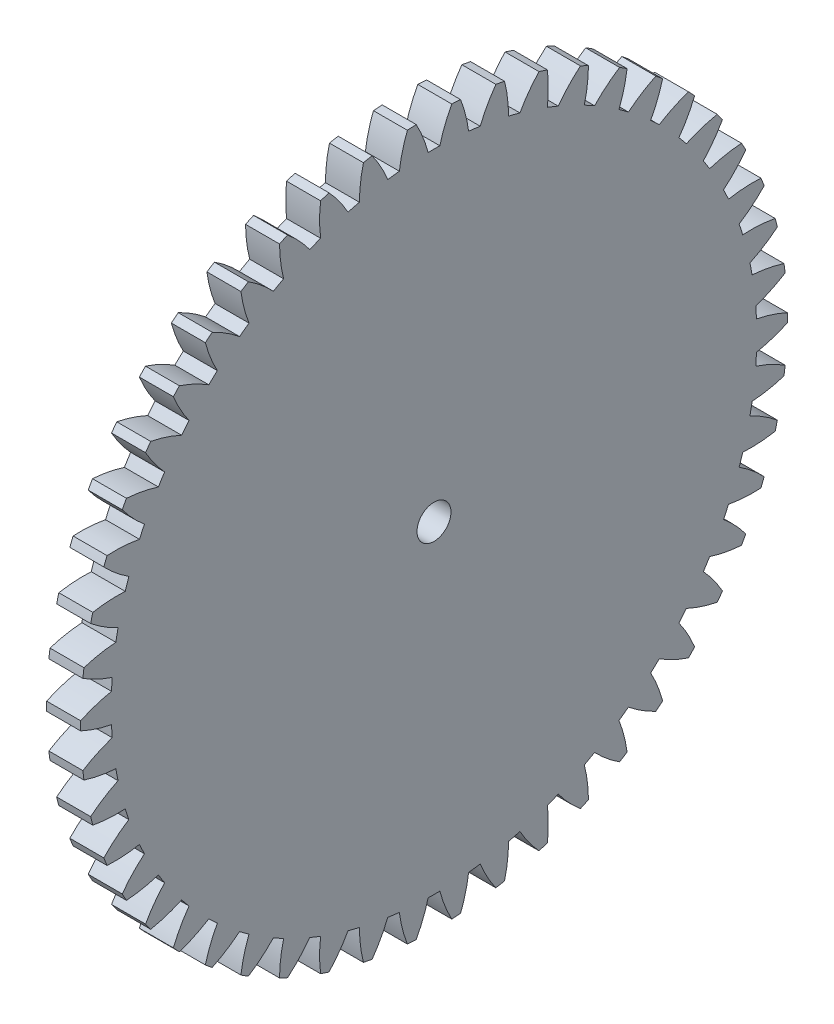
SolidWorks part; units mm, degrees
ref_plane "Plane1" through (0, 0, 0) normal (0, 0, 1) x (1, 0, 0)
ref_plane "Plane2" through (0, 0, 0) normal (0, 1, 0) x (1, 0, 0)
ref_plane "Plane3" through (0, 0, 0) normal (1, 0, 0) x (0, 0, -1)
sketch "HoldingSke" plane through (0, 0, 0) normal (0, 1, 0) x (1, 0, 0)
  line L0 (0, 0) -> (0.3214, -0.383)
  line L1 (-15, 0) -> (100, 0) construction
  line L2 (0, 0) -> (-2.1039, 2.3779)
  line L3 (0, 0) -> (-11.863, 4.5341)
  line L4 (0, 0) -> (5.5511, 6.6156)
  line L5 (0, 0) -> (-46.8476, -17.4728)
  line L6 (0, 0) -> (-4.1448, -2.7965)
  line L7 (-2.1039, 2.3779) -> (8.6586, 51.2059)
  line L8 (-76.2, 54.61) -> (-75.3, 54.61)
  line L9 (-71.009, 38.7566) -> (-53.1078, 45.2721)
  line L10 (-76.2, 71.12) -> (104.1128, 71.12)
  line L11 (0, 0) -> (-5, 0)
  line L12 (-76.2, 101.6) -> (-76.133, 101.6)
  line L13 (24.9733, 27.94) -> (52.9518, 28.4284)
  line L14 (24.9733, 27.94) -> (24.9743, 27.94)
  line L15 (24.9733, 27.94) -> (100.4006, 29.5858)
  line L16 (-63.627, -2) -> (-12.827, -2)
  circle A0 centre (0, 0) radius 2.5
  circle A1 centre (0, 0) radius 37.5
  circle A2 centre (0, 0) radius 37.5
  circle A3 centre (0, 0) radius 2.5
  dimension "MHD" = 75
  dimension "Hub_dia" = 75
  dimension "Bore" = 5
  dimension "MBD" = 5
  dimension "Num_teeth" = 50
  dimension "Pitch_radius" = 180.3128
  dimension "Pitch" = 0.5
  dimension "Width" = 5
  dimension "Overall_len" = 50
  dimension "Show_teeth" = 50
  dimension "Thickness" = 5
  dimension "OAL" = 50.0001
  dimension "T_dim" = 0.9
  dimension "Ap" = 20
  dimension "H" = 19.05
  dimension "Backlash" = 0.067
  dimension "Addendum_fac" = 1
  dimension "Dedendum_fac" = 1.25
  dimension "Clearance_fac" = 0.25
  dimension "Dedendum_add" = 0.001
  dimension "Module" = 2
sketch "BasProSke" plane through (0, 0, 0) normal (0, 1, 0) x (1, 0, 0)
  line L0 (-10, 0) -> (60, 0) construction
  line L1 (0, 0) -> (0, 52)
  line L2 (0, 0) -> (5, 0)
  line L3 (5, 0) -> (5, 52)
  line L4 (5, 52) -> (0, 52)
  dimension "Diameter" = 104
  dimension "Thickness" = 5
revolve "Base-Revolve" add sketch "BasProSke" angle 360 about L0
sketch "TooCutSke" plane through (0, 0, 0) normal (1, 0, 0) x (0, 0, -1)
  line L1 (0, 0) -> (0, 107) construction
  line L2 (0, 0) -> (-1.6878, 49.9715) construction
  line L3 (0, 0) -> (-6.2764, 99.7605) construction
  line L4 (-1.6878, 49.9715) -> (-3.1382, 49.8803) construction
  arc A0 (0.8606, 47.4912) -> (-0.8606, 47.4912) centre (0, 0) ccw
  arc A1 (2.629, 51.9589) -> (-2.629, 51.9589) centre (0, 0) ccw
  circle A2 centre (0, 0) radius 50 construction
  circle A3 centre (0, 0) radius 46.9846 construction
  arc A4 (-0.8606, 47.4912) -> (-2.629, 51.9589) centre (-20.2064, 42.4176) ccw
  arc A5 (2.629, 51.9589) -> (0.8606, 47.4912) centre (20.2064, 42.4176) ccw
  dimension "Root_dia" = 94.998
  dimension "Overcut_dia" = 104.0508
  dimension "Pitch_dia" = 100
  dimension "Base_dia" = 93.9693
  dimension "Flank_rad" = 20
  dimension "Half_ang" = 3.6
  dimension "Half_CT" = 1.4533
extrude "ToothCut" cut sketch "TooCutSke" along normal through all
fillet "Breaks" [suppressed] radius 0.04
fillet "RootFillets" [suppressed] radius 0.501
pattern_circular "TeethCuts" count 50 every 7.2 about axis through (-10, 0, 0) along (1, 0, 0) of "ToothCut", "RootFillets", "Breaks"
sketch "HubNeaOneSke" plane through (0, 0, 0) normal (-1, 0, 0) x (0, 0, 1)
  circle A0 centre (0, 0) radius 37.5
  dimension "Diameter" = 75
extrude "HubNearOne" [suppressed] add sketch "HubNeaOneSke" along normal blind 45.0001
sketch "HubNeaBotSke" plane through (0, 0, 0) normal (-1, 0, 0) x (0, 0, 1)
  circle A0 centre (0, 0) radius 37.5
  dimension "Diameter" = 75
extrude "HubNearBoth" [suppressed] add sketch "HubNeaBotSke" along normal blind 22.5
ref_plane "FarPln" through (5, 0, 0) normal (1, 0, 0) x (0, 0, -1)
sketch "HubFarSke" plane through (5, 0, 0) normal (1, 0, 0) x (0, 0, -1)
  circle A0 centre (0, 0) radius 37.5
  dimension "Diameter" = 75
extrude "HubFar" [suppressed] add sketch "HubFarSke" along normal blind 22.5
sketch "BorSke" plane through (0, 0, 0) normal (1, 0, 0) x (0, 0, -1)
  circle A0 centre (0, 0) radius 2.5
  dimension "Diameter" = 5
extrude "Bore" cut sketch "BorSke" along normal mid plane 100.0001
sketch "KeySke" plane through (0, 0, 0) normal (1, 0, 0) x (0, 0, -1)
  line L0 (-1, 0) -> (-1, 3.4)
  line L1 (-1, 3.4) -> (1, 3.4)
  line L2 (1, 3.4) -> (1, 0)
  line L3 (0, 0) -> (0, 34) construction
  line L4 (-1, 0) -> (1, 0)
  dimension "Offset" = 3.4
  dimension "Width" = 2
extrude "Keyway" [suppressed] cut sketch "KeySke" along normal mid plane 100.0001
pattern_circular "Keyway2" [suppressed] count 2 every 90 about axis through (-10, 0, 0) along (1, 0, 0)
equation "' \"Module@HoldingSke\" = 6.35"
equation "' \"Num_teeth@HoldingSke\" = 12"
equation "' \"Ap@HoldingSke\" =  20"
equation "' \"Width@HoldingSke\" = 0.5 * 25.4"
equation "' \"Hub_dia@HoldingSke\"= 1 * 25.4"
equation "' \"Overall_len@HoldingSke\" = 1.0 * 25.4"
equation "' \"Bore@HoldingSke\" = 0.75 * 25.4"
equation "' \"T_dim@HoldingSke\" = 0.1 * 25.4"
equation "' \"Width@KeySke\" = 0.25 * 25.4"
equation "' \"Show_teeth@HoldingSke\" = 13"
equation "' \"Backlash@HoldingSke\" = 0.009 * 25.4"
equation "' \"Addendum_fac@HoldingSke\" = 1.0"
equation "' \"Dedendum_fac@HoldingSke\" = 1.25"
equation "' \"Dedendum_add@HoldingSke\" = 0.00005 * 25.4"
equation "' \"Clearance_fac@HoldingSke\" = 0.25"
equation "\"Pitch@HoldingSke\" = 1 / \"Module@HoldingSke\""
equation "\"Overcut_dia@TooCutSke\" = (\"Num_teeth@HoldingSke\" + 2 * \"Addendum_fac@HoldingSke\") / \"Pitch@HoldingSke\" + 0.002 * 25.4"
equation "\"Pitch_dia@TooCutSke\" = \"Num_teeth@HoldingSke\" / \"Pitch@HoldingSke\""
equation "\"Base_dia@TooCutSke\" = \"Num_teeth@HoldingSke\" / \"Pitch@HoldingSke\" * cos((\"Ap@HoldingSke\"  * 3.14159265 / 180))"
equation "\"Root_dia@TooCutSke\" = (\"Num_teeth@HoldingSke\" + 2) / \"Pitch@HoldingSke\" - 2 * (\"Addendum_fac@HoldingSke\" + \"Dedendum_fac@HoldingSke\") / \"Pitch@HoldingSke\" - \"Dedendum_add@HoldingSke\" * 2"
equation "\"Half_ang@TooCutSke\" = 180 / \"Num_teeth@HoldingSke\""
equation "\"Half_CT@TooCutSke\" = \"Num_teeth@HoldingSke\" / \"Pitch@HoldingSke\" * sin((3.14159265 / 2 / \"Num_teeth@HoldingSke\")) / 2 - 7 * \"Backlash@HoldingSke\" / 4"
equation "\"Flank_rad@TooCutSke\" = \"Num_teeth@HoldingSke\" / \"Pitch@HoldingSke\" / 5"
equation "\"Radius@RootFillets\" = \"Clearance_fac@HoldingSke\" / \"Pitch@HoldingSke\" + \"Dedendum_add@HoldingSke\""
equation "\"Break_rad@Breaks\" = 0.02 / \"Pitch@HoldingSke\""
equation "\"Thickness@HoldingSke\" = \"Width@HoldingSke\""
equation "\"OAL@HoldingSke\" = \"Thickness@HoldingSke\""
equation "\"MHD@HoldingSke\" = (\"Num_teeth@HoldingSke\" + 2) / \"Pitch@HoldingSke\" - 2 * (\"Addendum_fac@HoldingSke\" + \"Dedendum_fac@HoldingSke\")  / \"Pitch@HoldingSke\" - \"Dedendum_add@HoldingSke\" * 2"
equation "\"MBD@HoldingSke\" = (\"Num_teeth@HoldingSke\" + 2) / \"Pitch@HoldingSke\" - 2 * (\"Addendum_fac@HoldingSke\" + \"Dedendum_fac@HoldingSke\")  / \"Pitch@HoldingSke\" - \"Dedendum_add@HoldingSke\" * 2 - 0.002 * 25.4"
equation "\"MHD@HoldingSke\" = ((sgn( \"MHD@HoldingSke\" - \"Hub_dia@HoldingSke\" )-1)*( \"MHD@HoldingSke\" - \"Hub_dia@HoldingSke\" ))/-2+ \"Hub_dia@HoldingSke\""
equation "\"MBD@HoldingSke\" = ((sgn( \"MBD@HoldingSke\" - \"Bore@HoldingSke\" )-1)*( \"MBD@HoldingSke\" - \"Bore@HoldingSke\" ))/-2+ \"Bore@HoldingSke\""
equation "\"OAL@HoldingSke\" = ((sgn( \"OAL@HoldingSke\" - \"Overall_len@HoldingSke\" )+1)*( \"OAL@HoldingSke\" - \"Overall_len@HoldingSke\" ))/2 + \"Overall_len@HoldingSke\" + 0.000002 * 25.4"
equation "\"Num_teeth@TeethCuts\" = int( \"Show_teeth@HoldingSke\" ) + 1"
equation "\"Num_teeth@TeethCuts\" = ((sgn( \"Num_teeth@TeethCuts\" - \"Num_teeth@HoldingSke\" )-1)*( \"Num_teeth@TeethCuts\" - \"Num_teeth@HoldingSke\" ))/-2+ \"Num_teeth@HoldingSke\""
equation "\"Num_teeth@TeethCuts\" = ((sgn( \"Num_teeth@TeethCuts\" - 2.0)+1)*( \"Num_teeth@TeethCuts\" - 2.0))/2 +2.0"
equation "\"Angle@TeethCuts\" = 360.0 / \"Num_teeth@HoldingSke\""
equation "\"Diameter@BasProSke\" = (\"Num_teeth@HoldingSke\" + 2 * \"Addendum_fac@HoldingSke\") / \"Pitch@HoldingSke\""
equation "\"Thickness@BasProSke\"  = \"Thickness@HoldingSke\""
equation "' \"Fillet_rad@BasProSke\" =  \"Thickness@HoldingSke\" * 0.05"
equation "\"MHD@HoldingSke\" = ((sgn( \"MHD@HoldingSke\" - \"Root_dia@TooCutSke\" )-1)*( \"MHD@HoldingSke\" - \"Root_dia@TooCutSke\" ))/-2+ \"Root_dia@TooCutSke\""
equation "\"Diameter@HubNeaOneSke\" = \"MHD@HoldingSke\""
equation "\"Length@HubNearOne\" = \"OAL@HoldingSke\" - \"Thickness@BasProSke\""
equation "\"Diameter@HubNeaBotSke\" = \"MHD@HoldingSke\""
equation "\"Length@HubNearBoth\" = ( \"OAL@HoldingSke\" - \"Thickness@BasProSke\" ) / 2.0"
equation "\"Thickness@FarPln\" = \"Thickness@BasProSke\""
equation "\"Diameter@HubFarSke\" = \"MHD@HoldingSke\""
equation "\"Length@HubFar\" = ( \"OAL@HoldingSke\" - \"Thickness@BasProSke\" ) / 2.0"
equation "\"Diameter@BorSke\" = \"MBD@HoldingSke\""
equation "\"D1@Bore\" = \"OAL@HoldingSke\" * 2.0"
equation "\"D1@Keyway\" = \"OAL@HoldingSke\" * 2.0"
equation "\"Offset@KeySke\" = \"T_dim@HoldingSke\" + \"MBD@HoldingSke\" / 2.0"
